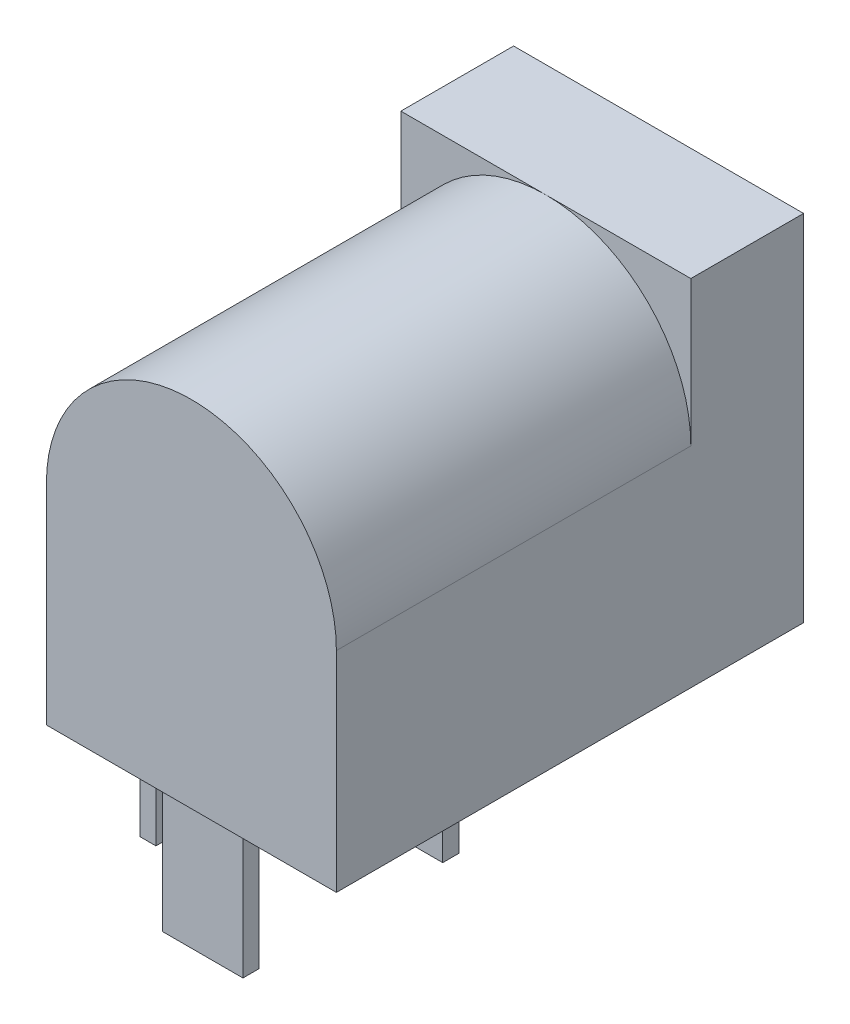
SolidWorks part; units mm, degrees
ref_plane "Front Plane" through (0, 0, 0) normal (0, 0, 1) x (1, 0, 0)
ref_plane "Top Plane" through (0, 0, 0) normal (0, 1, 0) x (1, 0, 0)
ref_plane "Right Plane" through (0, 0, 0) normal (1, 0, 0) x (0, 0, -1)
sketch "Sketch1" plane through (0, 0, 0) normal (0, 0, 1) x (1, 0, 0)
  line L1 (-4.5, 0) -> (4.5, 0)
  line L2 (-4.5, 0) -> (-4.5, 11)
  line L3 (-4.5, 11) -> (4.5, 11)
  line L4 (4.5, 0) -> (4.5, 11)
  point P4 (0, 0)
  dimension "D1" = 9
  dimension "D2" = 11
extrude "Extrude1" add sketch "Sketch1" along normal blind 14.5
sketch "Sketch2" plane through (0, 0, 0) normal (0, -1, 0) x (1, 0, 0)
  line L1 (-1.25, 13.65) -> (1.25, 13.65)
  line L2 (-1.25, 13.65) -> (-1.25, 14.15)
  line L3 (-1.25, 14.15) -> (1.25, 14.15)
  line L4 (1.25, 13.65) -> (1.25, 14.15)
  line L5 (1.25, 13.9) -> (3.2431, 13.9) construction
  line L6 (-4.5, 0) -> (4.5, 0) construction
  line L7 (1.25, 7.7) -> (2.977, 7.7) construction
  line L8 (-1.25, 7.95) -> (1.25, 7.95)
  line L9 (-1.25, 7.95) -> (-1.25, 7.45)
  line L10 (-1.25, 7.45) -> (1.25, 7.45)
  line L11 (1.25, 7.95) -> (1.25, 7.45)
  line L12 (-3.65, 10.7) -> (-1.7205, 10.7) construction
  line L13 (-4.15, 11.95) -> (-3.65, 11.95)
  line L14 (-4.15, 11.95) -> (-4.15, 9.45)
  line L15 (-4.15, 9.45) -> (-3.65, 9.45)
  line L16 (-3.65, 11.95) -> (-3.65, 9.45)
  line L18 (-4.5, 14.5) -> (-4.5, 0) construction
  point P4 (0, 13.65)
  point P15 (0, 7.45)
  dimension "D1" = 2.5
  dimension "D2" = 0.5
  dimension "D3" = 13.9
  dimension "D4" = 2.5
  dimension "D5" = 0.5
  dimension "D6" = 7.7
  dimension "D7" = 0.5
  dimension "D8" = 2.5
  dimension "D9" = 10.7
  dimension "D10" = 0.35
extrude "Extrude2" add sketch "Sketch2" along normal blind 4.1
sketch "Sketch3" plane through (0, 0, 14.5) normal (0, 0, 1) x (1, 0, 0)
  line L0 (4.5, 0) -> (4.5, 11) construction
  line L1 (4.5, 11) -> (-4.5, 11) construction
  line L2 (-4.5, 11) -> (-4.5, 0) construction
  line L3 (4.5, 6.5) -> (5.9159, 6.5)
  line L4 (5.9159, 6.5) -> (5.9159, 12.1707)
  line L5 (5.9159, 12.1707) -> (-5.2814, 12.1707)
  line L6 (-5.2814, 12.1707) -> (-5.2814, 6.5)
  line L7 (-5.2814, 6.5) -> (-4.5, 6.5)
  arc A0 (4.5, 6.5) -> (-4.5, 6.5) centre (0, 6.5) ccw
extrude "Cut-Extrude1" cut sketch "Sketch3" against normal blind 11
sketch "Sketch4" plane through (0, 0, 0) normal (0, 0, -1) x (-1, 0, 0)
  circle A0 centre (0, 6.5) radius 2.1
  dimension "D1" = 4.2
extrude "Cut-Extrude2" cut sketch "Sketch4" against normal blind 10
